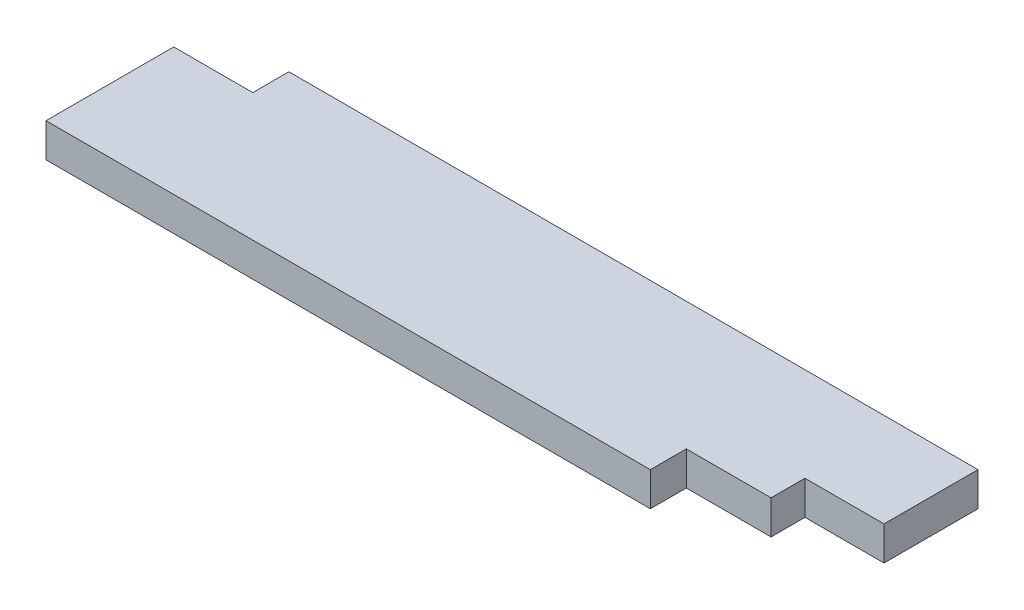
SolidWorks part; units mm, degrees
material "Pine"
ref_plane "Front Plane" through (0, 0, 0) normal (0, 0, 1) x (1, 0, 0)
ref_plane "Top Plane" through (0, 0, 0) normal (0, 1, 0) x (1, 0, 0)
ref_plane "Right Plane" through (0, 0, 0) normal (1, 0, 0) x (0, 0, -1)
sketch "Sketch1" plane through (0, 0, 0) normal (0, 1, 0) x (1, 0, 0)
  line L1 (0, 0) -> (863.6, 0)
  line L2 (0, 0) -> (0, 184.15)
  line L3 (0, 184.15) -> (863.6, 184.15)
  line L4 (863.6, 0) -> (863.6, 184.15)
  dimension "D1" = 184.15
  dimension "D2" = 863.6
extrude "Boss-Extrude1" add sketch "Sketch1" along normal blind 38.1
sketch "Sketch3" plane through (0, 38.1, 0) normal (0, 1, 0) x (1, 0, 0)
  line L0 (0, 184.15) -> (0, 0) construction
  line L13 (0, 184.15) -> (88.9, 184.15)
  line L14 (0, 184.15) -> (0, 143.5735)
  line L15 (0, 143.5735) -> (88.9, 143.5735)
  line L16 (88.9, 184.15) -> (88.9, 143.5735)
  line L17 (863.6, 0) -> (863.6, 184.15) construction
  line L18 (863.6, 78.486) -> (774.7, 78.486)
  line L19 (863.6, 78.486) -> (863.6, 0)
  line L20 (774.7, 40.386) -> (679.45, 40.386)
  line L21 (774.7, 78.486) -> (774.7, 40.386)
  line L25 (679.45, 0) -> (679.45, 40.386)
  line L26 (0, 0) -> (863.6, 0) construction
  line L28 (679.45, 0) -> (863.6, 0)
  line L30 (0, 92.075) -> (1033.2949, 92.075) construction
  line L31 (863.6, 184.15) -> (0, 184.15) construction
  point P23 (774.7, 59.436)
  point P24 (819.15, 78.486)
  dimension "D1" = 65.0875
  dimension "D2" = 78.486
  dimension "D3" = 88.9
  dimension "D4" = 38.1
  dimension "D5" = 65.0875
  dimension "D6" = 88.9
  dimension "D7" = 774.7
  dimension "D8" = 184.15
extrude "Cut-Extrude1" cut sketch "Sketch3" against normal through all
